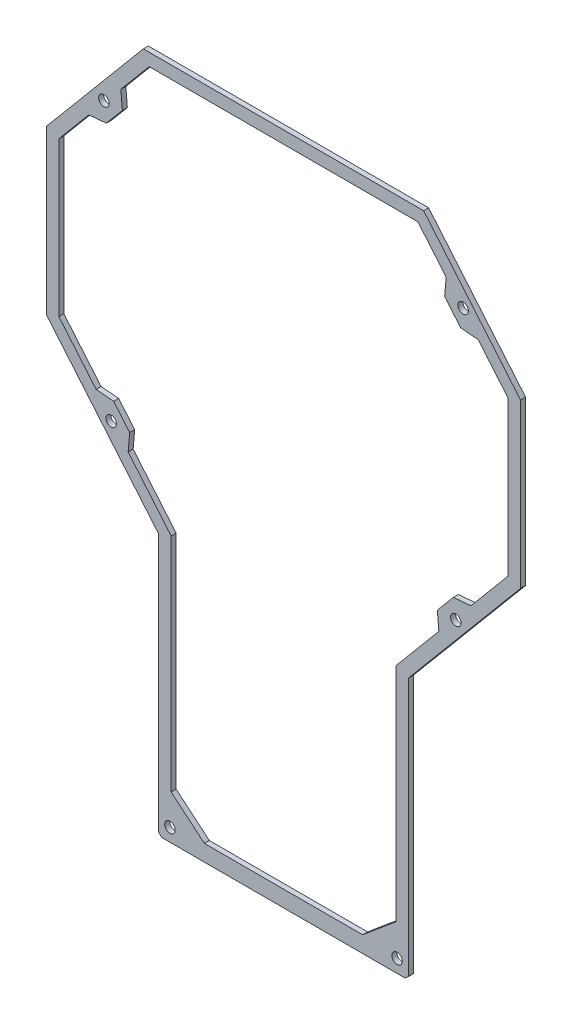
SolidWorks part; units mm, degrees
ref_plane "Plano frontal" through (0, 0, 0) normal (0, 0, 1) x (1, 0, 0)
ref_plane "Plano superior" through (0, 0, 0) normal (0, 1, 0) x (1, 0, 0)
ref_plane "Plano direito" through (0, 0, 0) normal (1, 0, 0) x (0, 0, -1)
sketch "Esboço1" plane through (0, 0, 0) normal (0, 0, 1) x (1, 0, 0)
  line L0 (56.4637, 135.1597) -> (-55.8644, 135.1597)
  line L1 (-55.8644, 135.1597) -> (-94.7003, 88.8768)
  line L2 (-94.7003, 88.8768) -> (-94.7003, 23.4903)
  line L3 (-94.7003, 23.4903) -> (-49.7003, -30.1386)
  line L4 (-49.7003, -30.1386) -> (-49.7003, -133.7325)
  line L5 (-49.7003, -133.7325) -> (-48.3802, -134.8403)
  line L6 (-48.3802, -134.8403) -> (48.9795, -134.8403)
  line L7 (50.2997, -133.7325) -> (48.9795, -134.8403)
  line L8 (50.2997, -30.1386) -> (50.2997, -133.7325)
  line L9 (95.2997, 23.4903) -> (50.2997, -30.1386)
  line L10 (95.2997, 88.8768) -> (95.2997, 23.4903)
  line L11 (56.4637, 135.1597) -> (95.2997, 88.8768)
  point P9 (0.2997, -134.8403)
  point P10 (0.2997, 135.1597)
extrude "Ressalto-extrusão1" add sketch "Esboço1" along normal blind 2
sketch "Esboço2" plane through (0, 0, 2) normal (0, 0, 1) x (1, 0, 0)
  line L0 (0.2997, -140.2297) -> (0.2997, 174.3695) construction
  line L1 (56.4637, 135.1597) -> (-55.8644, 135.1597) construction
  line L2 (-94.7003, 88.8768) -> (-94.7003, 23.4903) construction
  line L3 (-48.3802, -134.8403) -> (48.9795, -134.8403) construction
  line L5 (-94.7003, 23.4903) -> (-49.7003, -30.1386) construction
  line L8 (-49.7003, -30.1386) -> (-49.7003, -133.7325) construction
  line L9 (50.2997, -133.7325) -> (50.2997, -30.1386) construction
  circle A0 centre (-71.6727, 109.2987) radius 2.1
  circle A1 centre (-45.2003, -129.6103) radius 2.1
  circle A2 centre (45.7997, -129.6103) radius 2.1
  circle A3 centre (72.272, 109.2987) radius 2.1
  circle A4 centre (-68.7531, -0.4316) radius 2.1
  circle A5 centre (69.3525, -0.4316) radius 2.1
  dimension "D1" = 25.861
  dimension "D2" = 4.5
  dimension "D3" = 4.5
  dimension "D7" = 23.0276
  dimension "D8" = 5.23
  dimension "D4" = 4.5
extrude "Corte-extrusão1" cut sketch "Esboço2" against normal up to next
sketch "Esboço3" plane through (0, 0, 2) normal (0, 0, 1) x (1, 0, 0)
  line L0 (0.2997, -138.0724) -> (0.2997, 160.776) construction
  line L1 (-53.5328, 130.1597) -> (-64.8796, 116.6372)
  line L2 (-64.8796, 116.6372) -> (-64.2633, 109.5931)
  line L3 (-64.2633, 109.5931) -> (-70.6759, 101.9508)
  line L4 (-70.6759, 101.9508) -> (-77.7201, 101.3345)
  line L5 (-53.5328, 130.1597) -> (54.1321, 130.1597)
  line L6 (-89.7003, 87.057) -> (-89.7003, 25.3102)
  line L7 (-89.7003, 25.3102) -> (-74.79, 7.5407)
  line L8 (-77.7201, 101.3345) -> (-89.7003, 87.057)
  line L9 (-44.7003, -117.1732) -> (-31.4077, -128.3271)
  line L10 (-31.4077, -128.3271) -> (32.007, -128.3271)
  line L11 (-74.79, 7.5407) -> (-67.7458, 6.9244)
  line L12 (-67.7458, 6.9244) -> (-61.334, -0.7169)
  line L13 (-61.334, -0.7169) -> (-61.9503, -7.7611)
  line L14 (-61.9503, -7.7611) -> (-44.7003, -28.3187)
  line L15 (-94.7003, 23.4903) -> (-49.7003, -30.1386) construction
  line L17 (62.5496, -7.7611) -> (45.2997, -28.3187)
  line L18 (45.2997, -28.3187) -> (45.2997, -117.1732)
  line L19 (61.9333, -0.7169) -> (62.5496, -7.7611)
  line L20 (68.3451, 6.9244) -> (61.9333, -0.7169)
  line L21 (-49.7003, -133.7325) -> (-48.3802, -134.8403) construction
  line L22 (75.3893, 7.5407) -> (68.3451, 6.9244)
  line L23 (-94.7003, 88.8768) -> (-94.7003, 23.4903) construction
  line L24 (-55.8644, 135.1597) -> (-94.7003, 88.8768) construction
  line L25 (90.2997, 25.3102) -> (75.3893, 7.5407)
  line L28 (45.2997, -117.1732) -> (32.007, -128.3271)
  line L29 (78.3194, 101.3345) -> (90.2997, 87.057)
  line L31 (90.2997, 87.057) -> (90.2997, 25.3102)
  line L32 (71.2752, 101.9508) -> (78.3194, 101.3345)
  line L33 (64.8626, 109.5931) -> (71.2752, 101.9508)
  line L34 (65.4789, 116.6372) -> (64.8626, 109.5931)
  line L35 (54.1321, 130.1597) -> (65.4789, 116.6372)
  line L37 (-44.7003, -28.3187) -> (-44.7003, -117.1732)
  line L38 (-49.7003, -30.1386) -> (-49.7003, -133.7325) construction
  circle A1 centre (-71.6727, 109.2987) radius 2.1 construction
  circle A2 centre (-68.7531, -0.4316) radius 2.1 construction
  point P29 (0.2997, -128.3271)
  point P33 (0.2997, 130.1597)
  dimension "D6" = 10
  dimension "D12" = 10
  dimension "D13" = 10
  dimension "D4" = 45
  dimension "D9" = 10
  dimension "D14" = 10
  dimension "D2" = 5
  dimension "D3" = 5
  dimension "D5" = 5
  dimension "D7" = 10
  dimension "D8" = 5
  dimension "D10" = 45
  dimension "D11" = 45
  dimension "D15" = 45
  dimension "D18" = 5
extrude "Corte-extrusão2" cut sketch "Esboço3" against normal blind 10
